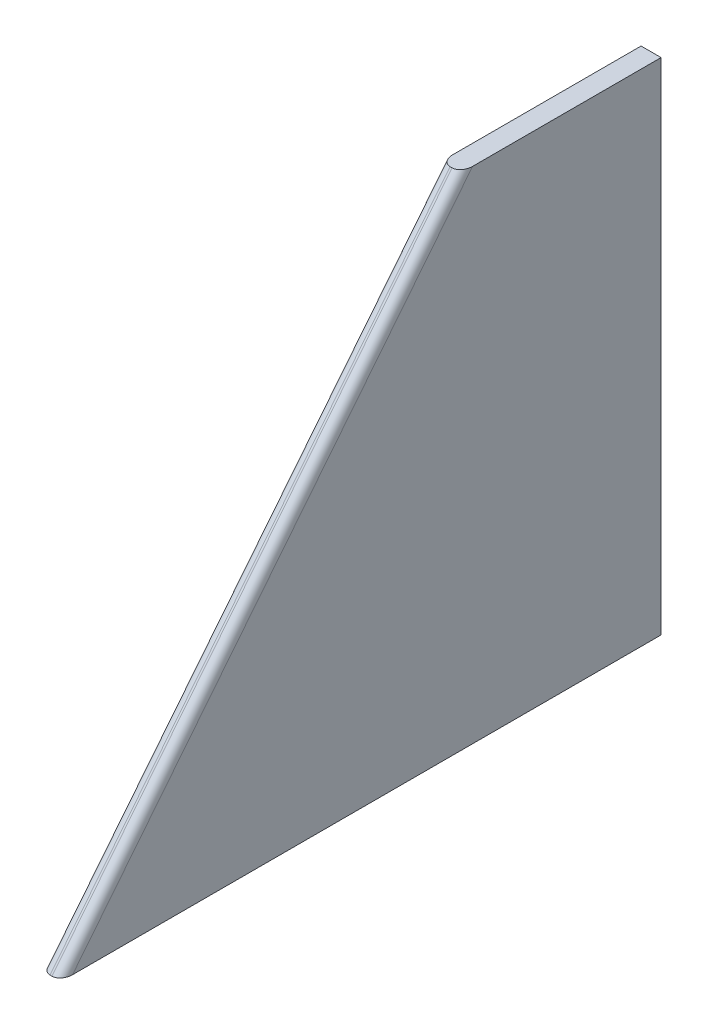
SolidWorks part; units mm, degrees
material "PS HI"
ref_plane "Front Plane" through (0, 0, 0) normal (0, 0, 1) x (1, 0, 0)
ref_plane "Top Plane" through (0, 0, 0) normal (0, 1, 0) x (1, 0, 0)
ref_plane "Right Plane" through (0, 0, 0) normal (1, 0, 0) x (0, 0, -1)
sketch "Sketch1" plane through (0, 0, 0) normal (1, 0, 0) x (0, 0, -1)
  line L0 (0, 0) -> (76.2, 0)
  line L1 (76.2, 0) -> (76.2, 63.5)
  line L2 (76.2, 63.5) -> (50.8, 63.5)
  line L3 (50.8, 63.5) -> (0, 0)
  point P3 (0, 0)
  point P6 (0, 0)
  point P7 (81.5338, 44.0871)
  point P8 (0, 0)
  point P9 (0, 0)
  dimension "D1" = 25.4
  dimension "D2" = 63.5
  dimension "D3" = 76.2
extrude "Boss-Extrude1" add sketch "Sketch1" along normal mid plane 2.54
fillet "Fillet1" radius 1.143 2 edges at (-1.27, 31.75, -25.4) (1.27, 31.75, -25.4)
